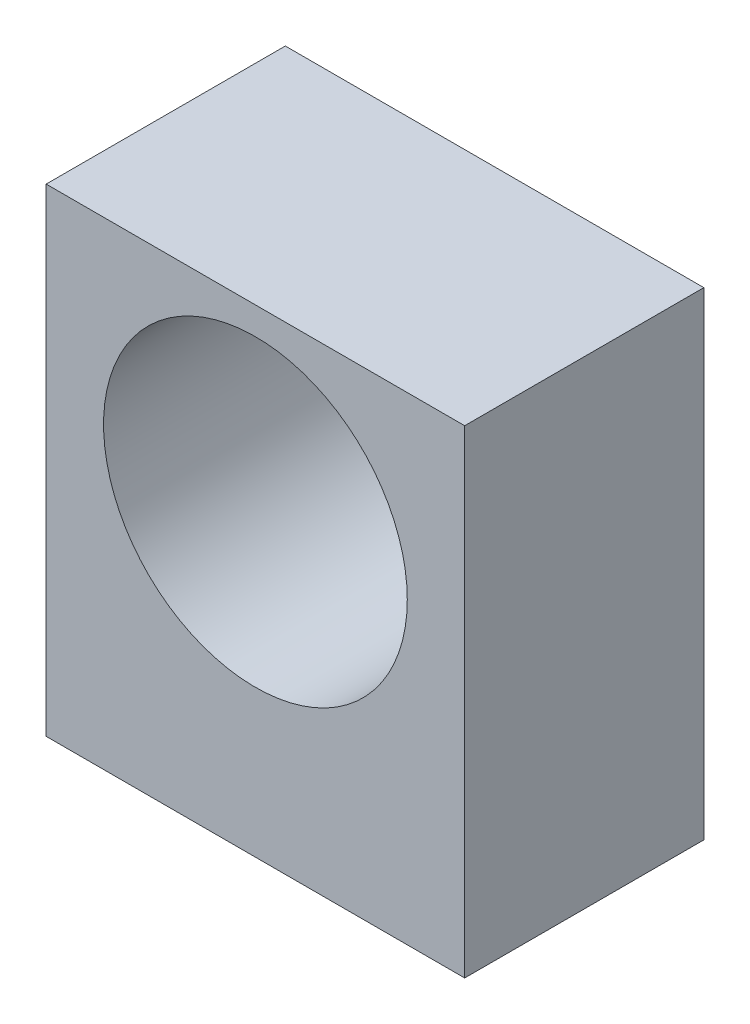
SolidWorks part; units mm, degrees
ref_plane "Front Plane" through (0, 0, 0) normal (0, 0, 1) x (1, 0, 0)
ref_plane "Top Plane" through (0, 0, 0) normal (0, 1, 0) x (1, 0, 0)
ref_plane "Right Plane" through (0, 0, 0) normal (1, 0, 0) x (0, 0, -1)
sketch "Sketch1" plane through (0, 0, 0) normal (0, 1, 0) x (1, 0, 0)
  line L1 (-16.3353, 9.1448) -> (18.6647, 9.1448)
  line L2 (-16.3353, 9.1448) -> (-16.3353, -10.8552)
  line L3 (-16.3353, -10.8552) -> (18.6647, -10.8552)
  line L4 (18.6647, 9.1448) -> (18.6647, -10.8552)
  dimension "D1" = 35
  dimension "D2" = 20
extrude "Boss-Extrude1" add sketch "Sketch1" along normal blind 40
sketch "Sketch2" plane through (0, 0, 10.8552) normal (0, 0, 1) x (1, 0, 0)
  line L0 (18.6647, 40) -> (18.6647, 0) construction
  line L1 (-16.3353, 0) -> (18.6647, 0) construction
  circle A0 centre (1.1647, 25) radius 12.7
  dimension "D1" = 17.5
  dimension "D2" = 25
extrude "Cut-Extrude1" cut sketch "Sketch2" against normal through all
sketch "Sketch3" plane through (0, 0, 0) normal (0, -1, 0) x (1, 0, 0)
  line L0 (18.6647, -9.1448) -> (-16.3353, -9.1448) construction
  line L1 (-16.3353, -9.1448) -> (-16.3353, 10.8552) construction
  line L2 (18.6647, 10.8552) -> (18.6647, -9.1448) construction
  circle A0 centre (-8.3353, 0.8552) radius 1.75
  circle A1 centre (10.6647, 0.8552) radius 1.75
  point P4 (-16.3353, 0.8552)
  dimension "D1" = 10
  dimension "D3" = 10
  dimension "D2" = 8
  dimension "D4" = 8
extrude "Cut-Extrude2" cut sketch "Sketch3" against normal blind 10
